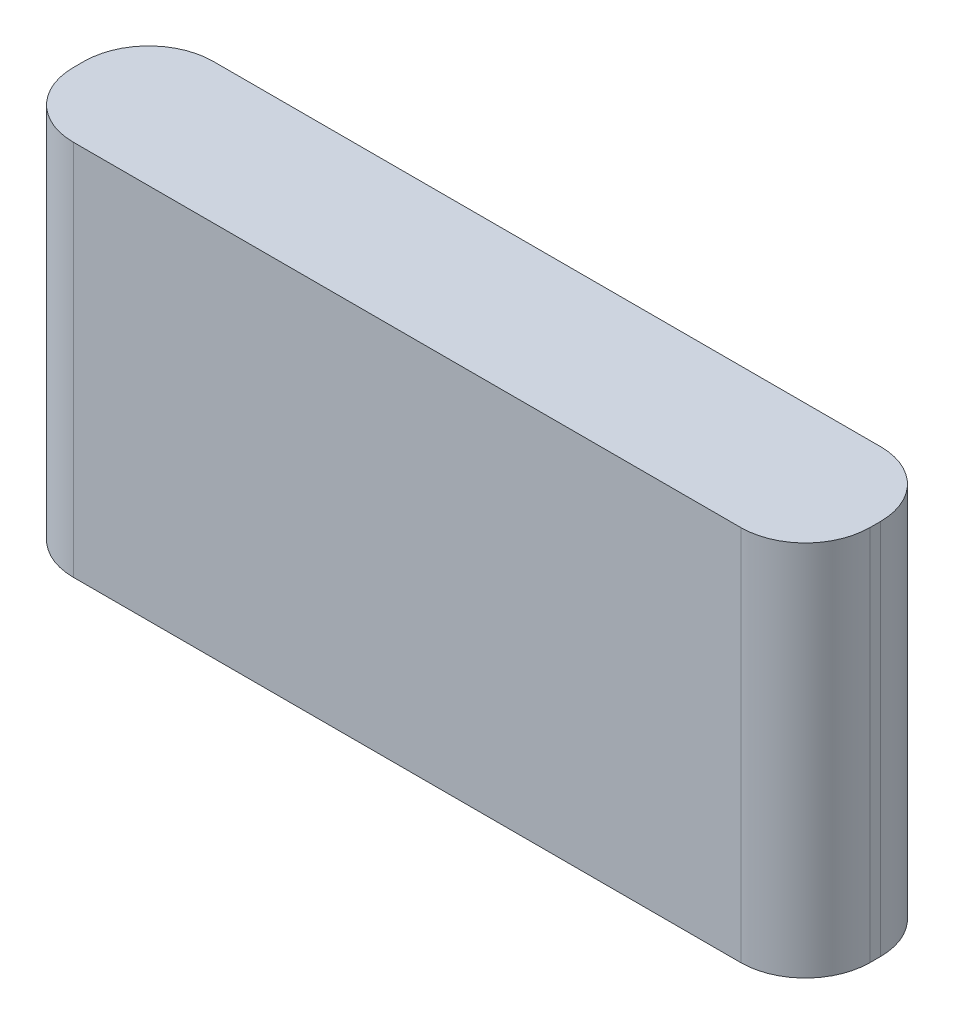
SolidWorks part; units mm, degrees
ref_plane "Front" through (0, 0, 0) normal (0, 0, 1) x (1, 0, 0)
ref_plane "Top" through (0, 0, 0) normal (0, 1, 0) x (1, 0, 0)
ref_plane "Right" through (0, 0, 0) normal (1, 0, 0) x (0, 0, -1)
sketch "Sketch1" plane through (0, 0, 0) normal (0, 0, 1) x (1, 0, 0)
  line L1 (-37, 17.5) -> (37, 17.5)
  line L2 (-37, 17.5) -> (-37, -17.5)
  line L3 (-37, -17.5) -> (37, -17.5)
  line L4 (37, 17.5) -> (37, -17.5)
  line L5 (-37, 17.5) -> (37, -17.5) construction
  line L6 (-37, -17.5) -> (37, 17.5) construction
  point P0 (0, 0)
  dimension "D1" = 74
  dimension "D2" = 35
extrude "Boss-Extrude1" add sketch "Sketch1" along normal blind 13
fillet "Fillet2" radius 6 4 edges at (-37, 0, 0) (-37, 0, 13) (37, 0, 0) (37, 0, 13)
